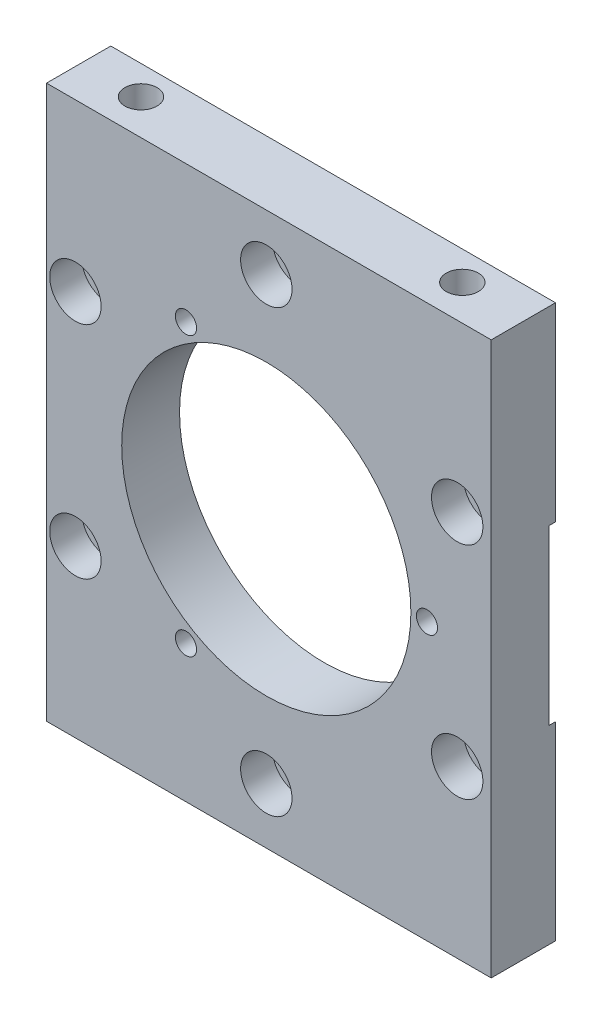
SolidWorks part; units mm, degrees
ref_plane "Alzado" through (0, 0, 0) normal (0, 0, 1) x (1, 0, 0)
ref_plane "Planta" through (0, 0, 0) normal (0, 1, 0) x (1, 0, 0)
ref_plane "Vista lateral" through (0, 0, 0) normal (1, 0, 0) x (0, 0, -1)
sketch "Croquis1" plane through (0, 0, 0) normal (0, 0, 1) x (1, 0, 0)
  line L0 (0, 0) -> (0, 34.3) construction
  line L1 (-46.8638, 0) -> (37.9436, 0) construction
  line L2 (0, 0) -> (0, -34.3) construction
  line L4 (-34.2, 43) -> (35, 43)
  line L5 (-34.2, 43) -> (-34.2, -43)
  line L6 (-34.2, -43) -> (35, -43)
  line L7 (35, 43) -> (35, -43)
  circle A0 centre (0, 0) radius 22.5
  circle A1 centre (0, 34.3) radius 2.75
  circle A2 centre (29.7047, 17.15) radius 2.75
  circle A3 centre (29.7047, -17.15) radius 2.75
  circle A4 centre (0, -34.3) radius 2.75
  circle A5 centre (-29.7047, -17.15) radius 2.75
  circle A6 centre (-29.7047, 17.15) radius 2.75
  point P0 (0, 0)
  dimension "D3" = 45
  dimension "D5" = 5.5
  dimension "D1" = 34.2
  dimension "D2" = 35
  dimension "D4" = 34.3
  dimension "D7" = 34.3
  dimension "D8" = 34.3
  dimension "D9" = 43
  dimension "D10" = 43
  dimension "D6" = 6
extrude "Saliente-Extruir1" add sketch "Croquis1" along normal mid plane 10
sketch "Croquis8" plane through (0, 0, 5) normal (0, 0, 1) x (1, 0, 0)
  circle A0 centre (-29.7047, 17.15) radius 4
  circle A1 centre (0, 34.3) radius 4
  circle A2 centre (29.7047, 17.15) radius 4
  circle A3 centre (29.7047, -17.15) radius 4
  circle A4 centre (0, -34.3) radius 4
  circle A5 centre (-29.7047, -17.15) radius 4
  dimension "D1" = 8
extrude "Cortar-Extruir3" cut sketch "Croquis8" against normal blind 5
hole_wizard "Taladro roscado M42" positions "Croquis10" profile "Croquis9" tap size "M4" standard "DIN" end condition through all
sketch "Croquis10" plane through (0, 0, 5) normal (0, 0, 1) x (1, 0, 0)
  line L0 (-12.5, 21.6506) -> (0, 0) construction
  line L1 (0, 0) -> (-12.5, -21.6506) construction
  line L2 (0, 0) -> (25, 0) construction
  point P0 (-12.5, 21.6506)
  point P1 (-12.5, -21.6506)
  point P3 (25, 0)
  dimension "D1" = 25
  dimension "D2" = 120
  dimension "D3" = 120
sketch "Croquis9" plane through (-12.5, 21.6506, 5) normal (1, 0, 0) x (0, -1, 0)
  line L0 (0, 0) -> (0, 10)
  line L1 (0, 10) -> (1.65, 10)
  line L2 (1.65, 10) -> (1.65, 0)
  line L5 (1.65, 0) -> (0, 0)
  line L11 (0, -6.35) -> (0, 107.95) construction
  dimension "Diámetro de perforador para roscar hasta el siguiente" = 3.3
  dimension "Profundidad de perforador para roscar hasta el siguiente" = 10
cosmetic thread "Rosca de taladro6" parameters "D2"=4
cosmetic thread "Rosca de taladro7" parameters "D2"=4
cosmetic thread "Rosca de taladro8" parameters "D2"=4
hole_wizard "Taladro roscado M62" positions "Croquis12" profile "Croquis11" tap size "M6" standard "DIN"
sketch "Croquis12" plane through (0, 43, 0) normal (0, 1, 0) x (-1, 0, 0)
  line L0 (-35, -5) -> (34.2, -5) construction
  line L1 (-35, 5) -> (-35, -5) construction
  line L2 (34.2, 5) -> (34.2, -5) construction
  point P0 (25, -0.5)
  point P1 (-25, -0.5)
  dimension "D1" = 4.5
  dimension "D2" = 4.5
  dimension "D3" = 50
  dimension "D4" = 10
  dimension "D5" = 9.2
sketch "Croquis11" plane through (-25, 43, -0.5) normal (1, 0, 0) x (0, 0, 1)
  line L0 (0, 0) -> (0, 19.5022)
  line L1 (0, 19.5022) -> (2.5, 18)
  line L2 (2.5, 18) -> (2.5, 0)
  line L5 (2.5, 0) -> (0, 0)
  line L10 (0, 19.5022) -> (-2.5, 18) construction
  line L11 (0, -6.35) -> (0, 107.95) construction
  dimension "Diámetro de perforador para roscar" = 5
  dimension "Profundidad de perforador para roscar" = 18
  dimension "Ángulo de perforador" = 118
cosmetic thread "Rosca de taladro9" parameters "D1"=12, "D2"=6
cosmetic thread "Rosca de taladro10" parameters "D1"=12, "D2"=6
hole_wizard "Taladro roscado M63" positions "Croquis14" profile "Croquis13" tap size "M6" standard "DIN"
sketch "Croquis14" plane through (0, -43, 0) normal (0, -1, 0) x (1, 0, 0)
  line L0 (-34.2, 5) -> (35, 5) construction
  line L1 (-34.2, 5) -> (-34.2, -5) construction
  point P0 (-25, -0.5)
  point P1 (25, -0.5)
  dimension "D1" = 5.5
  dimension "D2" = 5.5
  dimension "D3" = 50
  dimension "D4" = 9.2
sketch "Croquis13" plane through (-25, -43, -0.5) normal (1, 0, 0) x (0, 0, -1)
  line L0 (0, 0) -> (0, 19.5022)
  line L1 (0, 19.5022) -> (2.5, 18)
  line L2 (2.5, 18) -> (2.5, 0)
  line L5 (2.5, 0) -> (0, 0)
  line L10 (0, 19.5022) -> (-2.5, 18) construction
  line L11 (0, -6.35) -> (0, 107.95) construction
  dimension "Diámetro de perforador para roscar" = 5
  dimension "Profundidad de perforador para roscar" = 18
  dimension "Ángulo de perforador" = 118
cosmetic thread "Rosca de taladro11" parameters "D1"=12, "D2"=6
cosmetic thread "Rosca de taladro12" parameters "D1"=12, "D2"=6
sketch "Croquis15" plane through (0, 0, -5) normal (0, 0, -1) x (-1, 0, 0)
  circle A0 centre (0, 0) radius 37.5
  dimension "D1" = 75
extrude "Cortar-Extruir4" cut sketch "Croquis15" against normal blind 1
